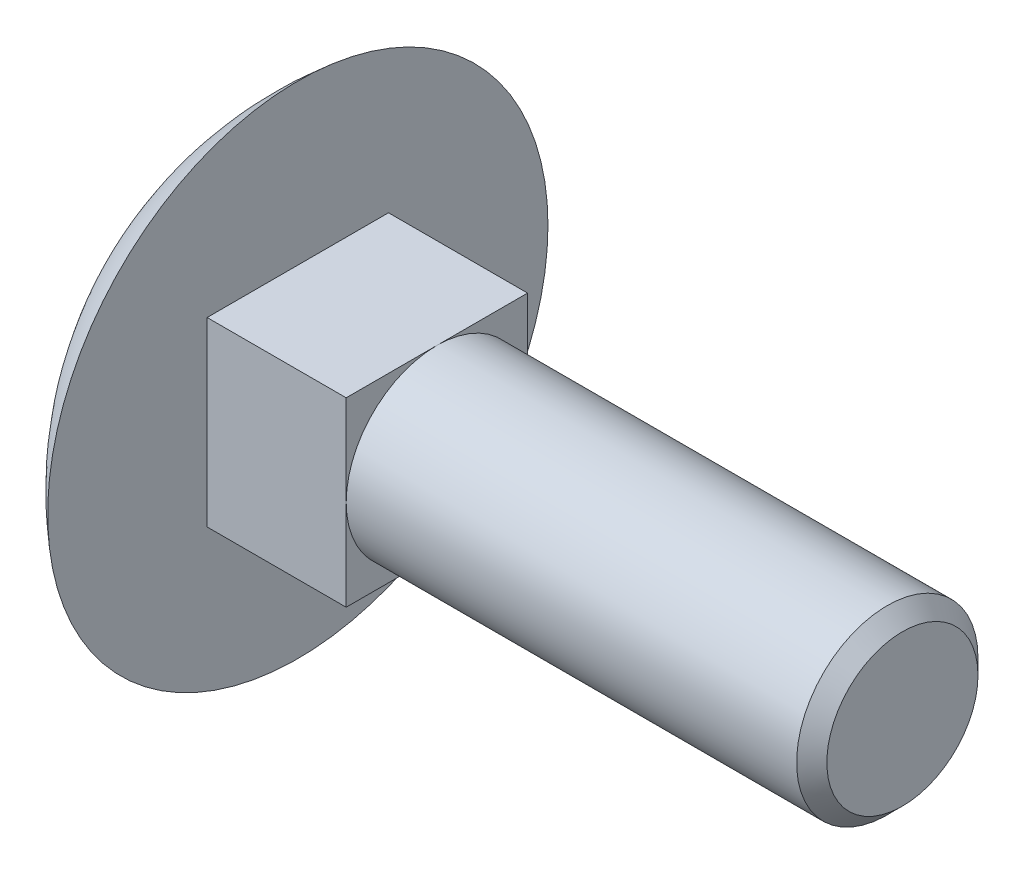
SolidWorks part; units mm, degrees
ref_plane "Ebene vorne" through (0, 0, 0) normal (0, 0, 1) x (1, 0, 0)
ref_plane "Ebene oben" through (0, 0, 0) normal (0, 1, 0) x (1, 0, 0)
ref_plane "Ebene rechts" through (0, 0, 0) normal (1, 0, 0) x (0, 0, -1)
sketch "Skizze1" plane through (0, 0, 0) normal (0, 1, 0) x (1, 0, 0)
  line L0 (0, 0) -> (0, 8.275)
  line L1 (0, 0) -> (-84.5143, 0) construction
  line L2 (-3.88, 0) -> (-3.88, 62.3962) construction
  line L3 (0, 0) -> (-3.88, 0)
  arc A0 (0, 8.275) -> (-3.88, 0) centre (6.8842, 0) ccw
  dimension "D1" = 3.88
  dimension "D2" = 8.275
revolve "Rotation1" add sketch "Skizze1" angle 360 about L1
sketch "Skizze2" plane through (0, 0, 0) normal (1, 0, 0) x (0, 0, -1)
  line L0 (-3, -3) -> (0, 0) construction
  line L1 (-3, 3) -> (3, 3)
  line L2 (-3, 3) -> (-3, -3)
  line L3 (-3, -3) -> (3, -3)
  line L4 (3, 3) -> (3, -3)
  line L5 (0, 0) -> (3, 3) construction
  dimension "D1" = 6
extrude "Linear austragen1" add sketch "Skizze2" along normal blind 4.6
sketch "Skizze3" plane through (4.6, 0, 0) normal (1, 0, 0) x (0, 0, -1)
  circle A0 centre (0, 0) radius 3
extrude "Linear austragen2" add sketch "Skizze3" along normal blind 15.4
chamfer "Fase1" distance 0.5 angle 45 1 edges at (20, 0, -3)
